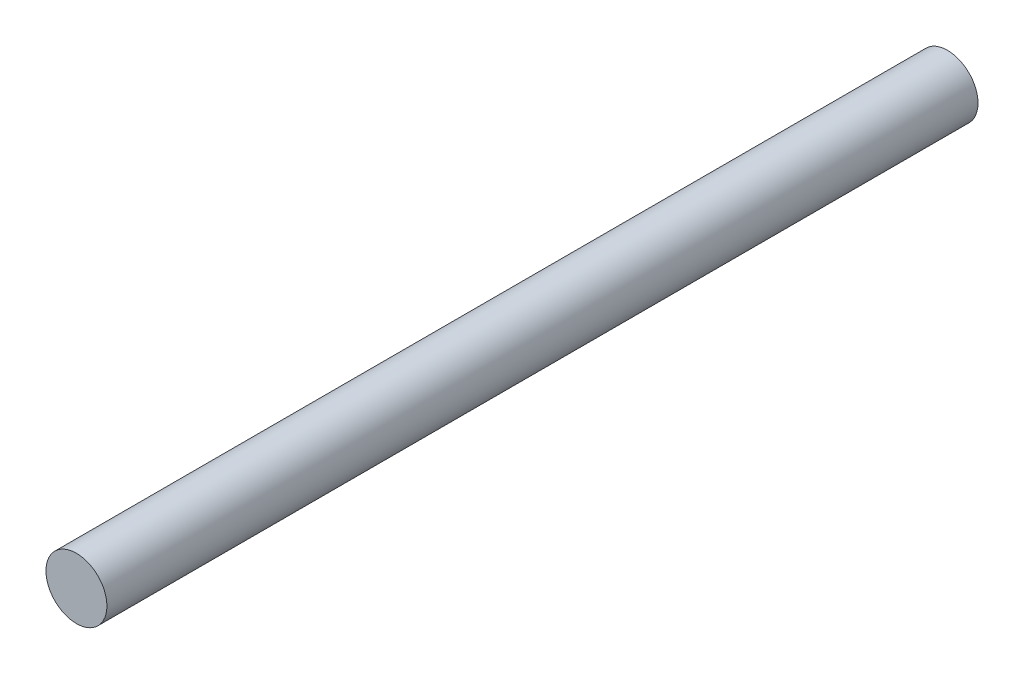
SolidWorks part; units mm, degrees
ref_plane "前视基准面" through (0, 0, 0) normal (0, 0, 1) x (1, 0, 0)
ref_plane "上视基准面" through (0, 0, 0) normal (0, 1, 0) x (1, 0, 0)
ref_plane "右视基准面" through (0, 0, 0) normal (1, 0, 0) x (0, 0, -1)
sketch "草图1" plane through (0, 0, 0) normal (0, 0, 1) x (1, 0, 0)
  circle A0 centre (0, 0) radius 1.4
  dimension "D1" = 2.8
extrude "凸台-拉伸1" add sketch "草图1" along normal blind 40
